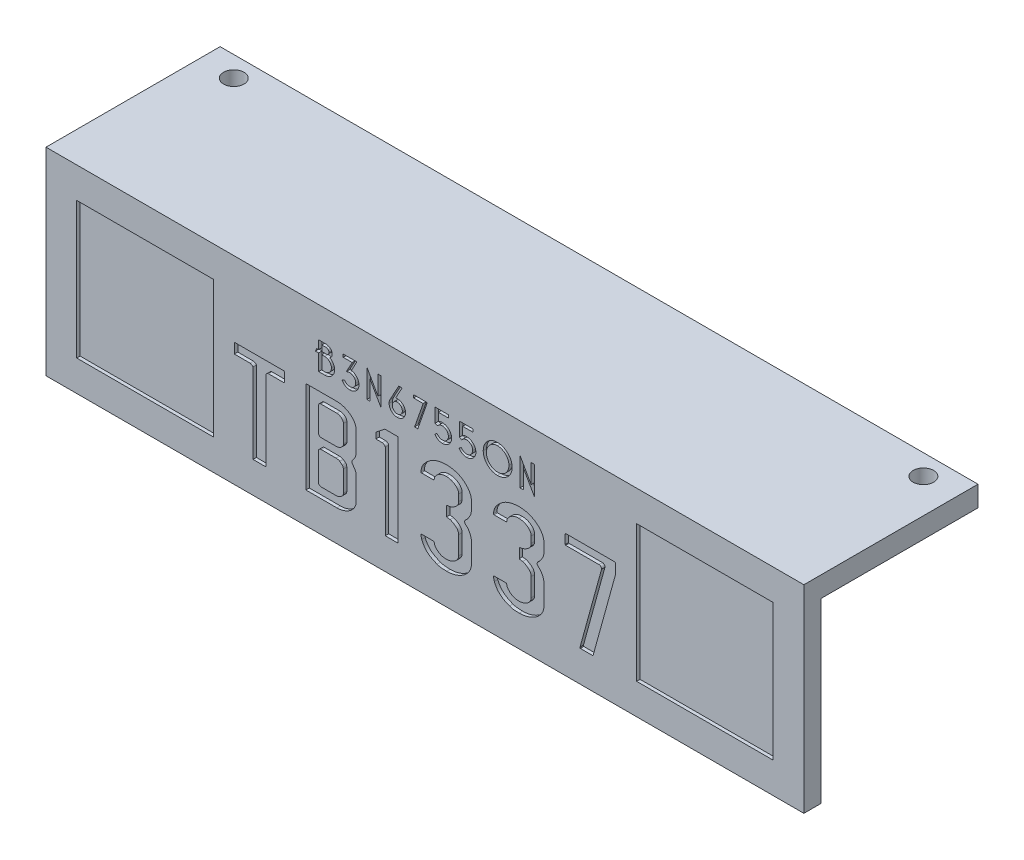
SolidWorks part; units mm, degrees
ref_plane "Front Plane" through (0, 0, 0) normal (0, 0, 1) x (1, 0, 0)
ref_plane "Top Plane" through (0, 0, 0) normal (0, 1, 0) x (1, 0, 0)
ref_plane "Right Plane" through (0, 0, 0) normal (1, 0, 0) x (0, 0, -1)
sketch "Sketch1" plane through (0, 0, 0) normal (0, 1, 0) x (1, 0, 0)
  line L1 (-43.7981, 22.4519) -> (67.2019, 22.4519)
  line L2 (-43.7981, 22.4519) -> (-43.7981, -3.0481)
  line L3 (-43.7981, -3.0481) -> (67.2019, -3.0481)
  line L4 (67.2019, 22.4519) -> (67.2019, -3.0481)
  circle A0 centre (-38.7981, 19.4519) radius 1.5
  circle A1 centre (62.2019, 19.4519) radius 1.5
  dimension "D3" = 3
  dimension "D4" = 101
  dimension "D6" = 5
  dimension "D7" = 3
  dimension "D1" = 25.5
  dimension "D2" = 3
  dimension "D5" = 5
extrude "Boss-Extrude1" add sketch "Sketch1" along normal blind 3
sketch "Sketch3" plane through (0, 0, 0) normal (0, -1, 0) x (1, 0, 0)
  line L0 (67.2019, 3.0481) -> (67.2019, -22.4519) construction
  line L1 (-43.7981, 3.0481) -> (67.2019, 3.0481)
  line L2 (-43.7981, 3.0481) -> (-43.7981, 0.5481)
  line L3 (-43.7981, 0.5481) -> (67.2019, 0.5481)
  line L4 (67.2019, 3.0481) -> (67.2019, 0.5481)
  dimension "D1" = 2.5
extrude "Boss-Extrude2" add sketch "Sketch3" along normal blind 26
sketch "Sketch4" plane through (0, 0, 3.0481) normal (0, 0, 1) x (1, 0, 0)
  line L0 (-43.7981, 3) -> (-43.7981, -26) construction
  line L1 (-39.2981, -1.5) -> (-19.2981, -1.5)
  line L2 (-39.2981, -1.5) -> (-39.2981, -21.5)
  line L3 (-39.2981, -21.5) -> (-19.2981, -21.5)
  line L4 (-19.2981, -1.5) -> (-19.2981, -21.5)
  line L6 (42.7019, -1.5) -> (62.7019, -1.5)
  line L7 (42.7019, -1.5) -> (42.7019, -21.5)
  line L8 (42.7019, -21.5) -> (62.7019, -21.5)
  line L9 (62.7019, -1.5) -> (62.7019, -21.5)
  point P4 (-39.2981, -11.5)
  point P7 (-43.7981, -11.5)
  dimension "D1" = 20
  dimension "D2" = 4.5
  dimension "D3" = 2
extrude "Cut-Extrude1" cut sketch "Sketch4" against normal blind 0.5
ref_plane "Plane2" through (-43.7981, 0, 0.5481) normal (1, 0, 0) x (0, 0, -1)
sketch "Sketch6" plane through (-43.7981, 0, 0.5481) normal (1, 0, 0) x (0, 0, -1)
  line L0 (0, 0) -> (5, 0)
  line L1 (23, 0) -> (0, 0) construction
  line L2 (5, 0) -> (0, -13)
  line L3 (0, -26) -> (0, 0) construction
  line L4 (0, -13) -> (0, 0)
  dimension "D1" = 5
extrude "Boss-Extrude3" add sketch "Sketch6" along normal blind 4 from offset 20.5
pattern_linear "LPattern1" count 4 spacing 22 along (1, 0, 0) of "Boss-Extrude3"
sketch "Sketch8" plane through (0, 0, 3.0481) normal (0, 0, 1) x (1, 0, 0)
  line L0 (-43.7981, -21.4493) -> (67.2019, -21.4493) construction
  line L1 (-43.7981, 3) -> (-43.7981, -26) construction
  line L2 (67.2019, 3) -> (67.2019, -26) construction
  line L3 (-43.7981, -5.5) -> (67.2019, -5.5) construction
  line L6 (-19.2981, -1.5) -> (-39.2981, -1.5) construction
  text T0 "TB1337" font "LICENSE PLATE USA" height 13.5
  text T1 "<b>B3N67550N</b>" font "Bellerose" height 4
  dimension "D1" = 4
extrude "Cut-Extrude3" cut sketch "Sketch8" against normal blind 0.5
